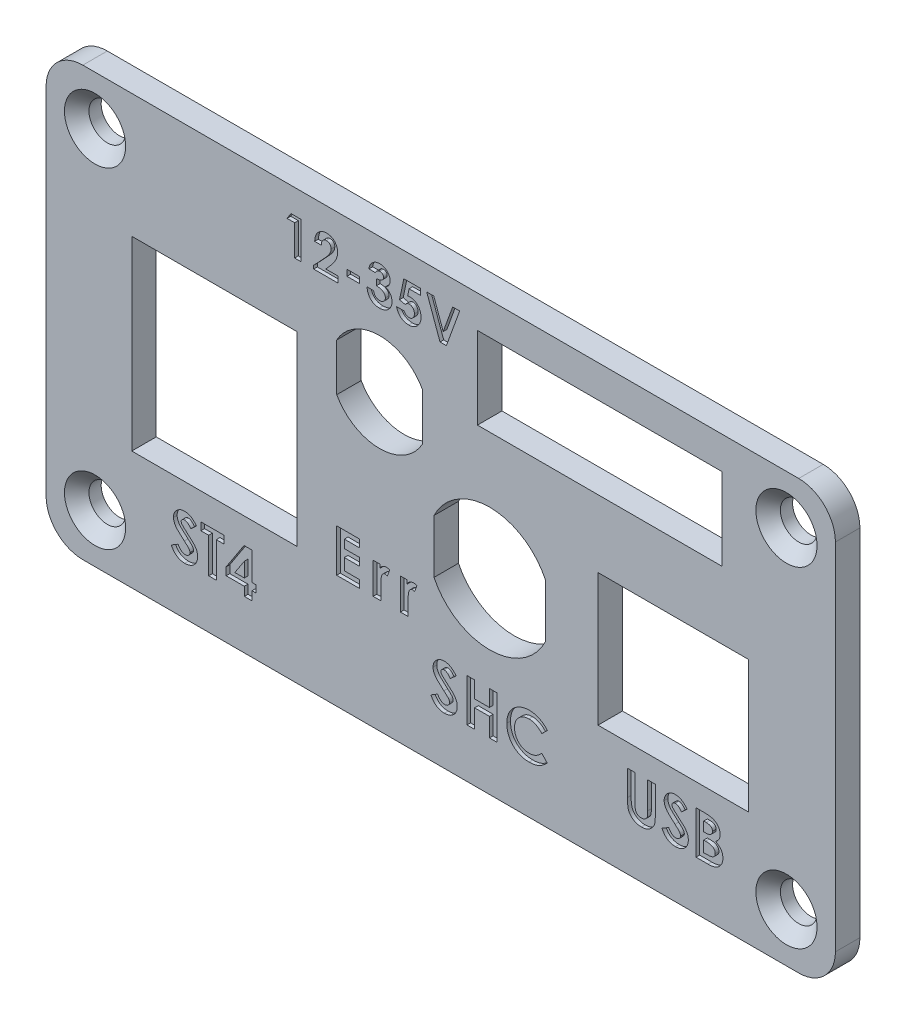
SolidWorks part; units mm, degrees
ref_plane "Plan de face" through (0, 0, 0) normal (0, 0, 1) x (1, 0, 0)
ref_plane "Plan de dessus" through (0, 0, 0) normal (0, 1, 0) x (1, 0, 0)
ref_plane "Plan de droite" through (0, 0, 0) normal (1, 0, 0) x (0, 0, -1)
sketch "Esquisse1" plane through (0, 0, 0) normal (0, 0, 1) x (1, 0, 0)
  line L0 (0, 0) -> (0, 34.1448) construction
  line L1 (-32.25, -17.5) -> (32.25, -17.5)
  line L2 (-32.25, -17.5) -> (-32.25, 17.5)
  line L3 (-32.25, 17.5) -> (32.25, 17.5)
  line L4 (32.25, -17.5) -> (32.25, 17.5)
  line L5 (-32.25, -17.5) -> (32.25, 17.5) construction
  line L6 (-32.25, 17.5) -> (32.25, -17.5) construction
  line L7 (3, 14.85) -> (23, 14.85)
  line L8 (3, 14.85) -> (3, 8.15)
  line L9 (3, 8.15) -> (23, 8.15)
  line L10 (23, 14.85) -> (23, 8.15)
  line L11 (3, 14.85) -> (23, 8.15) construction
  line L12 (3, 8.15) -> (23, 14.85) construction
  line L13 (-25.25, 7.39) -> (-11.75, 7.39)
  line L14 (-25.25, 7.39) -> (-25.25, -7.81)
  line L15 (-25.25, -7.81) -> (-11.75, -7.81)
  line L17 (-25.25, 7.39) -> (-11.75, -7.81) construction
  line L18 (-25.25, -7.81) -> (-11.75, 7.39) construction
  line L19 (12.85, 2.64) -> (25.15, 2.64)
  line L20 (12.85, 2.64) -> (12.85, -8.16)
  line L21 (12.85, -8.16) -> (25.15, -8.16)
  line L22 (25.15, 2.64) -> (25.15, -8.16)
  line L23 (12.85, 2.64) -> (25.15, -8.16) construction
  line L24 (12.85, -8.16) -> (25.15, 2.64) construction
  line L25 (0, 0) -> (12.0341, 0) construction
  line L26 (-11.75, 7.39) -> (-11.75, -7.81)
  line L27 (13, 11.5) -> (13, 13.2094) construction
  line L28 (8.55, -0.0191) -> (8.55, -4.4009)
  line L29 (-35.3333, -8.51) -> (35.4658, -8.51) construction
  line L30 (-34.4451, -10.11) -> (34.5636, -10.11) construction
  line L35 (-0.55, -0.0191) -> (-0.55, -4.4009)
  line L36 (4, -2.21) -> (4, -4.4898) construction
  line L37 (-8.5, 8.4265) -> (-8.5, 4.5535)
  line L38 (-1.5, 8.4265) -> (-1.5, 4.5535)
  line L39 (-5, 6.49) -> (-5, 0.2766) construction
  circle A3 centre (28.25, 13.5) radius 1.5
  circle A4 centre (-28.25, 13.5) radius 1.5
  arc A5 (-0.55, -4.4009) -> (8.55, -4.4009) centre (4, -2.21) ccw
  circle A6 centre (28.25, -13.5) radius 1.5
  circle A7 centre (-28.25, -13.5) radius 1.5
  arc A8 (8.55, -0.0191) -> (-0.55, -0.0191) centre (4, -2.21) ccw
  arc A9 (-8.5, 4.5535) -> (-1.5, 4.5535) centre (-5, 6.49) ccw
  arc A10 (-1.5, 8.4265) -> (-8.5, 8.4265) centre (-5, 6.49) ccw
  circle A11 centre (-5, 6.49) radius 5 construction
  point P0 (0, 0)
  point P8 (19, -8.16)
  point P10 (-18.5, -7.81)
  point P11 (12.6415, 13.2094)
  point P16 (13, 11.5)
  point P21 (-18.5, -0.21)
  point P26 (19, -2.76)
  point P45 (13, 14.85)
  point P53 (-35.3333, -8.51)
  point P55 (-34.4451, -10.11)
  dimension "D4" = 3
  dimension "D7" = 27
  dimension "D8" = 9.1
  dimension "D13" = 10.1
  dimension "D14" = 19
  dimension "D20" = 8
  dimension "D25" = 10
  dimension "D1" = 56.5
  dimension "D2" = 64.5
  dimension "D3" = 35
  dimension "D5" = 12.3
  dimension "D6" = 10.8
  dimension "D9" = 15.2
  dimension "D10" = 13.5
  dimension "D11" = 20
  dimension "D12" = 6.7
  dimension "D15" = 18.5
  dimension "D16" = 13
  dimension "D17" = 7
  dimension "D18" = 6.3
  dimension "D19" = 6
  dimension "D21" = 4
  dimension "D22" = 10.11
  dimension "D23" = 5
  dimension "D24" = 15
  dimension "D29" = 8.3
  dimension "D30" = 5.75
  dimension "D31" = 1.6
extrude "base" add sketch "Esquisse1" along normal blind 2
fillet "Congé1" radius 3 4 edges at (-32.25, -17.5, 1) (32.25, -17.5, 1) (32.25, 17.5, 1) (-32.25, 17.5, 1)
sketch "Esquisse2" plane through (0, 0, 2) normal (0, 0, 1) x (1, 0, 0)
  line L0 (-13.25, 12.5) -> (2.0242, 12.5) construction
  line L1 (-29.25, -17.5) -> (29.25, -17.5) construction
  line L2 (-32.25, 14.5) -> (-32.25, -14.5) construction
  line L3 (-9.7461, -8.2309) -> (-1.1204, -8.2309) construction
  line L4 (-1.5035, -13.5) -> (9.5035, -13.5) construction
  line L7 (4, -2.21) -> (4, -4.4898) construction
  line L8 (12.0844, -13.5) -> (26.0421, -13.5) construction
  line L9 (-24.9959, -13.5) -> (-12.0915, -13.5) construction
  text T0 "<b>12-35V</b>" font "Century Gothic" height 3
  text T1 "<b>Err</b>" font "Century Gothic" height 3.5
  text T2 "<b>SHC</b>" font "Century Gothic" height 3.5
  text T3 "USB" font "Century Gothic" height 3.5
  text T4 "ST4" font "Century Gothic" height 3.5
  point P4 (-1.6466, 12.5)
  point P5 (-10.386, -12.3613)
  point P12 (0.8966, -12.2226)
  point P13 (-1.1204, -8.51)
  point P14 (-2.7161, -12.5)
  point P15 (8.2394, -12.5)
  point P17 (-9.7461, -8.51)
  point P18 (0, 0)
  point P19 (0, 0)
  point P22 (4, -13.5)
  point P23 (-3.0322, -12.5)
  point P26 (19.0632, -13.5)
  point P29 (-18.5437, -13.5)
  point P30 (-25.3119, -15.4495)
  point P31 (-8.826, -12.5526)
  point P32 (14.8759, -13.5)
  point P33 (22.9345, -13.3954)
  point P35 (-11.1435, -12.816)
  point P36 (-22.7445, -12.342)
  point P37 (-24.3112, -12.2366)
  point P38 (-12.0915, -12.8687)
  point P39 (-12.7763, -12.7633)
  point P40 (-24.55, -13.3217)
  point P41 (-24.9959, -12.816)
  point P42 (26.0421, -13.2374)
  point P43 (12.9271, -13.5)
  point P44 (12.0844, -13.5)
  point P45 (9.5035, -13.5)
  point P46 (2.0242, 12.5)
  dimension "D1" = 30
  dimension "D2" = 19
  dimension "D3" = 4
extrude "texte" cut sketch "Esquisse2" against normal blind 0.3
chamfer "fraisurage vis" distance 1 angle 45 4 edges at (29.75, 13.5, 2) (-26.75, 13.5, 2) (26.75, -13.5, 2) (-29.75, -13.5, 2)
